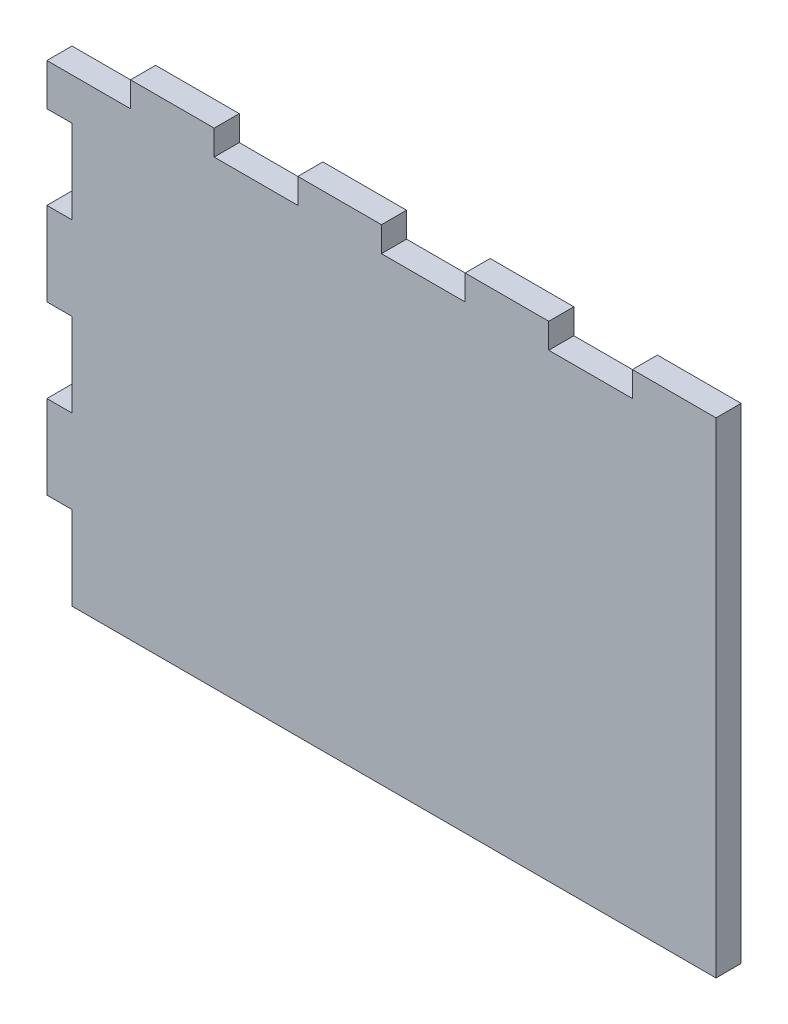
SolidWorks part; units mm, degrees
ref_plane "Plan de face" through (0, 0, 0) normal (0, 0, 1) x (1, 0, 0)
ref_plane "Plan de dessus" through (0, 0, 0) normal (0, 1, 0) x (1, 0, 0)
ref_plane "Plan de droite" through (0, 0, 0) normal (1, 0, 0) x (0, 0, -1)
sketch "Esquisse1" plane through (0, 0, 0) normal (0, 0, 1) x (1, 0, 0)
  line L1 (0, 0) -> (80, 0)
  line L2 (0, 0) -> (0, -58)
  line L3 (0, -58) -> (80, -58)
  line L4 (80, 0) -> (80, -58)
  dimension "D1" = 80
  dimension "D2" = 58
extrude "Boss.-Extru.1" add sketch "Esquisse1" along normal blind 3
sketch "Esquisse2" plane through (0, 0, 3) normal (0, 0, 1) x (1, 0, 0)
  line L1 (0, 0) -> (10, 0)
  line L2 (0, 0) -> (0, -3)
  line L3 (0, -3) -> (10, -3)
  line L4 (10, 0) -> (10, -3)
  dimension "D1" = 10
  dimension "D2" = 3
extrude "Enlèv. mat.-Extru.1" cut sketch "Esquisse2" against normal through all
pattern_linear "Répétition linéaire1" count 4 spacing 20 along (1, 0, 0) of "Enlèv. mat.-Extru.1"
sketch "Esquisse3" plane through (0, 0, 3) normal (0, 0, 1) x (1, 0, 0)
  line L1 (0, -58) -> (3, -58)
  line L2 (0, -58) -> (0, -48)
  line L3 (0, -48) -> (3, -48)
  line L4 (3, -58) -> (3, -48)
  dimension "D1" = 3
  dimension "D2" = 10
extrude "Enlèv. mat.-Extru.2" cut sketch "Esquisse3" against normal through all
pattern_linear "Répétition linéaire2" count 3 spacing 20 along (0, 1, 0) of "Enlèv. mat.-Extru.2"
